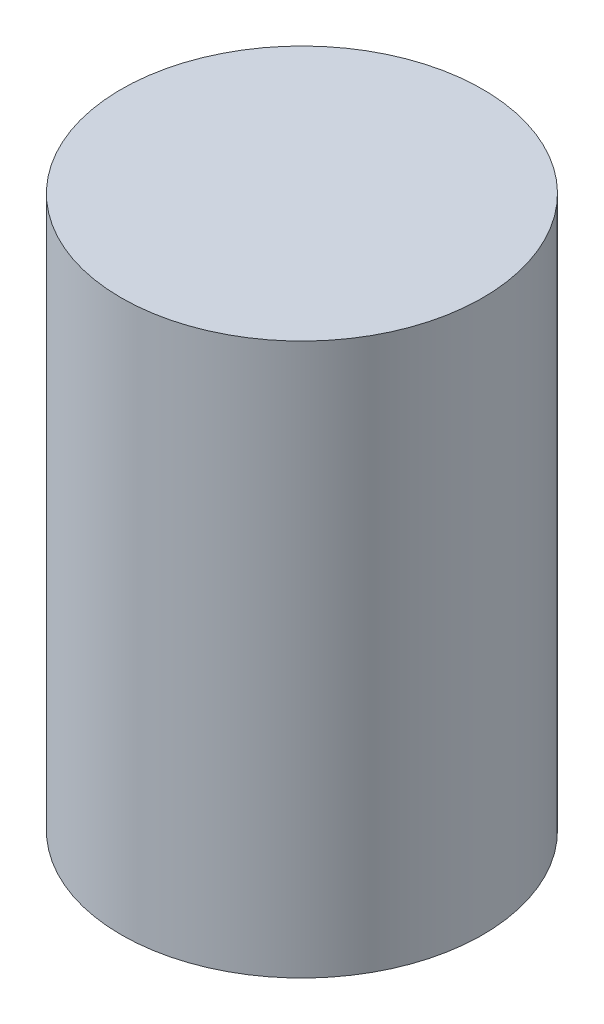
SolidWorks part; units mm, degrees
ref_plane "Front" through (0, 0, 0) normal (0, 0, 1) x (1, 0, 0)
ref_plane "Top" through (0, 0, 0) normal (0, 1, 0) x (1, 0, 0)
ref_plane "Right" through (0, 0, 0) normal (1, 0, 0) x (0, 0, -1)
sketch "Sketch1" plane through (0, 0, 0) normal (0, 1, 0) x (1, 0, 0)
  circle A0 centre (0, 0) radius 1.9
extrude "Boss-Extrude2" add sketch "Sketch1" along normal blind 5.8
